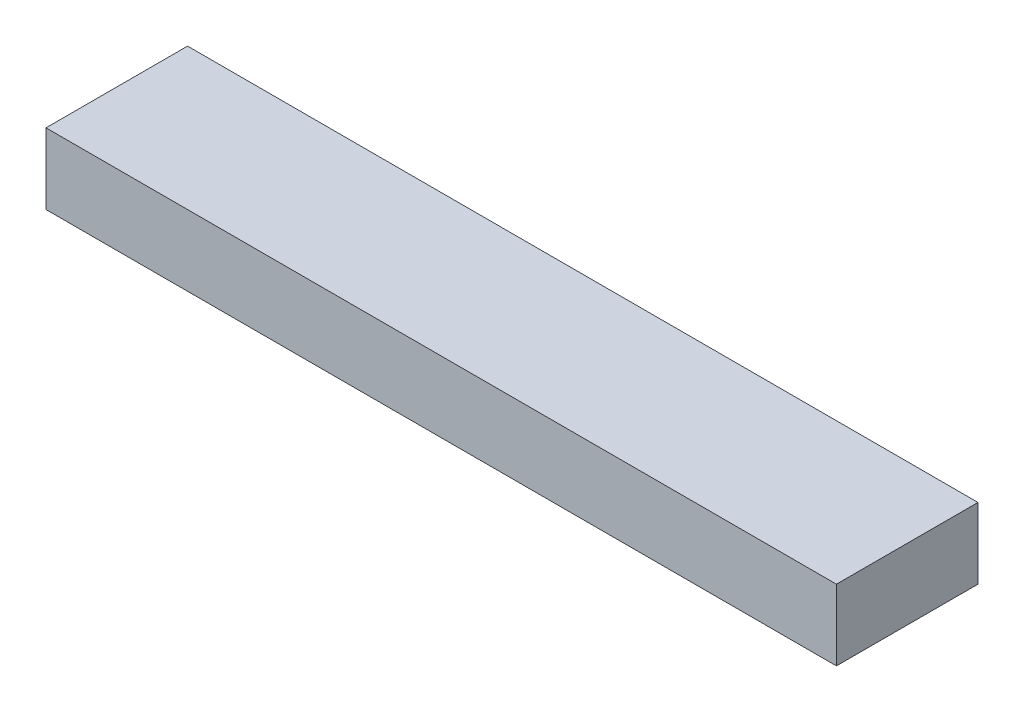
SolidWorks part; units mm, degrees
material "Pine"
ref_plane "Front Plane" through (0, 0, 0) normal (0, 0, 1) x (1, 0, 0)
ref_plane "Top Plane" through (0, 0, 0) normal (0, 1, 0) x (1, 0, 0)
ref_plane "Right Plane" through (0, 0, 0) normal (1, 0, 0) x (0, 0, -1)
sketch "Sketch1" plane through (0, 0, 0) normal (0, 1, 0) x (1, 0, 0)
  line L1 (0, 0) -> (212.725, 0)
  line L2 (0, 0) -> (0, 38.1)
  line L3 (0, 38.1) -> (212.725, 38.1)
  line L4 (212.725, 0) -> (212.725, 38.1)
  dimension "D1" = 38.1
  dimension "D2" = 212.725
extrude "Boss-Extrude1" add sketch "Sketch1" along normal blind 19.05
